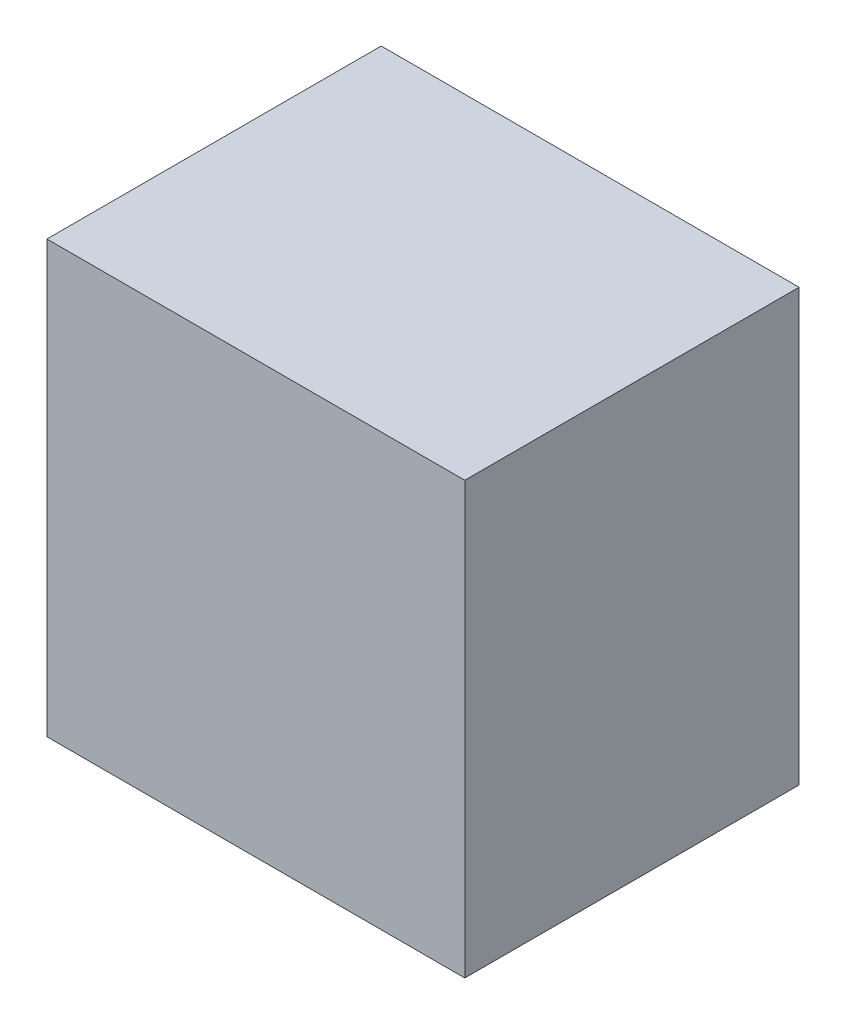
SolidWorks part; units mm, degrees
ref_plane "Front Plane" through (0, 0, 0) normal (0, 0, 1) x (1, 0, 0)
ref_plane "Top Plane" through (0, 0, 0) normal (0, 1, 0) x (1, 0, 0)
ref_plane "Right Plane" through (0, 0, 0) normal (1, 0, 0) x (0, 0, -1)
sketch "Sketch1" plane through (0, 0, 0) normal (0, 1, 0) x (1, 0, 0)
  line L1 (0, 0) -> (190, 0)
  line L2 (0, 0) -> (0, 152)
  line L3 (0, 152) -> (190, 152)
  line L4 (190, 0) -> (190, 152)
  dimension "D1" = 152
  dimension "D2" = 190
extrude "Boss-Extrude1" add sketch "Sketch1" along normal blind 196
